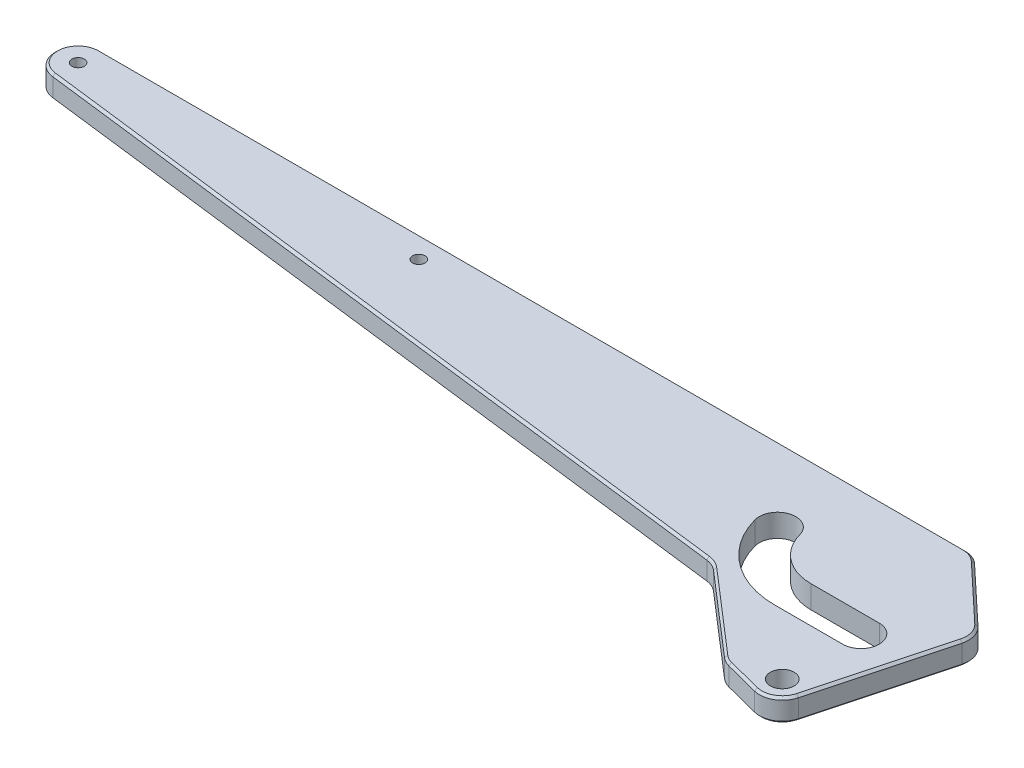
SolidWorks part; units mm, degrees
ref_plane "Front Plane" through (0, 0, 0) normal (0, 0, 1) x (1, 0, 0)
ref_plane "Top Plane" through (0, 0, 0) normal (0, 1, 0) x (1, 0, 0)
ref_plane "Right Plane" through (0, 0, 0) normal (1, 0, 0) x (0, 0, -1)
sketch "Sketch1" plane through (0, 0, 0) normal (0, 1, 0) x (1, 0, 0)
  line L3 (-390, 90) -> (34.4682, 90)
  line L4 (-391.2187, 70.0745) -> (-60, 29.406)
  line L5 (9.6593, -2.5882) -> (34.4682, 90)
  line L6 (-2.499, -9.6827) -> (-20, -5.1659)
  line L7 (-20, -5.1659) -> (-60, 29.406)
  arc A2 (-2.499, -9.6827) -> (9.6593, -2.5882) centre (0, 0) ccw
  arc A3 (-390, 90) -> (-391.2187, 70.0745) centre (-390, 80) ccw
  dimension "D1" = 20
  dimension "D2" = 390
  dimension "D3" = 80
  dimension "D4" = 7
  dimension "D5" = 75
  dimension "D6" = 20
  dimension "D7" = 40
extrude "Boss-Extrude1" add sketch "Sketch1" along normal mid plane 10
sketch "Slot Path" plane through (0, 0, 0) normal (0, 1, 0) x (1, 0, 0)
  line L0 (-30, 34.641) -> (0, 34.641)
  line L1 (0, -5.5) -> (0, 5.5) construction
  line L2 (-5.5, 0) -> (5.5, 0) construction
  arc A0 (-30, 34.641) -> (-58.9778, 56.8764) centre (-30, 64.641) cw
  dimension "D1" = 30
  dimension "D2" = 34.641
sketch "Sketch4" plane through (0, 5, 0) normal (0, 1, 0) x (1, 0, 0)
  line L30 (-30, 26.591) -> (0, 26.591)
  line L31 (-30, 42.691) -> (0, 42.691)
  arc A52 (-66.7535, 54.793) -> (-30, 26.591) centre (-30, 64.641) ccw
  arc A53 (-51.2021, 58.9599) -> (-30, 42.691) centre (-30, 64.641) ccw
  arc A54 (-66.7535, 54.793) -> (-51.2021, 58.9599) centre (-58.9778, 56.8764) cw
  arc A55 (0, 26.591) -> (0, 42.691) centre (0, 34.641) ccw
extrude "Slot" cut sketch "Sketch4" against normal through all
hole_wizard "Ø10.5 (10.5) Diameter Hole1" positions "Sketch9" profile "Sketch10" hole size "Ø10.5" standard "ANSI Metric"
sketch "Sketch9" plane through (0, 5, 0) normal (0, 1, 0) x (1, 0, 0)
  point P0 (0, 0)
sketch "Sketch10" plane through (0, 5, 0) normal (1, 0, 0) x (0, 0, 1)
  line L0 (0, 0) -> (0, 18.1545)
  line L1 (0, 18.1545) -> (5.25, 15)
  line L2 (5.25, 15) -> (5.25, 0)
  line L5 (5.25, 0) -> (0, 0)
  line L10 (0, 18.1545) -> (-5.25, 15) construction
  line L11 (0, -6.35) -> (0, 107.95) construction
  dimension "Hole Dia." = 10.5
  dimension "Hole Depth" = 15
  dimension "Drill Angle" = 118
hole_wizard "CBORE for M5 SHCS2" positions "Sketch14" profile "Sketch15" counterbore size "M5" standard "ANSI Metric"
sketch "Sketch14" plane through (0, -5, 0) normal (0, -1, 0) x (-1, 0, 0)
  arc A0 (391.2187, 70.0745) -> (390, 90) centre (390, 80) ccw construction
  point P0 (390, 80)
  point P2 (240, 80)
  dimension "D1" = 150
sketch "Sketch15" plane through (-390, -5, -80) normal (1, 0, 0) x (0, 0, -1)
  line L0 (0, 0) -> (0, 23.2524)
  line L1 (0, 23.2524) -> (2.75, 21.6)
  line L2 (2.75, 21.6) -> (2.75, 5)
  line L3 (2.75, 5) -> (5, 5)
  line L4 (5, 5) -> (5, 0)
  line L5 (5, 0) -> (0, 0)
  line L10 (0, 23.2524) -> (-2.75, 21.6) construction
  line L11 (0, -6.35) -> (0, 107.95) construction
  dimension "Hole Dia." = 5.5
  dimension "Hole Depth" = 21.6
  dimension "C'Bore Dia." = 10
  dimension "C'Bore Depth" = 5
  dimension "Drill Angle" = 118
sketch "Sketch13" plane through (0, 5, 0) normal (0, 1, 0) x (1, 0, 0)
  line L0 (-5.5318, 90) -> (34.4682, 90)
  line L1 (34.4682, 90) -> (-390, 90) construction
  line L2 (9.6593, -2.5882) -> (34.4682, 90) construction
  line L3 (34.4682, 90) -> (26.4297, 60)
  line L4 (26.4297, 60) -> (-5.5318, 90)
  dimension "D1" = 30
  dimension "D2" = 40
extrude "Cut-Extrude3" cut sketch "Sketch13" against normal through all
fillet "Fillet1" radius 10 4 edges at (-5.5318, 0, -90) (26.4297, 0, -60) (-20, 0, 5.1659) (-60, 0, -29.406)
chamfer "Chamfer1" distance 1 angle 45 24 edges at (-10.1155, -5, 7.717) (-19.8744, -5, 4.9261) (-39.7354, -5, -11.8914) (-60.1834, -5, -28.9925) (-227.1189, -5, -49.9256) (-399.9813, -5, -80.6105) (-199.7449, -5, -90) (-5.8096, -5, -89.2982) (9.7094, -5, -75.6941) (24.8381, -5, -59.5464) (17.2698, -5, -25.8147) (5.0399, -5, 8.6371) (-399.9813, 5, -80.6105) (-227.1189, 5, -49.9256) (-60.1834, 5, -28.9925) (-39.7354, 5, -11.8914) (-19.8744, 5, 4.9261) (-10.1155, 5, 7.717) (5.0399, 5, 8.6371) (17.2698, 5, -25.8147) (24.8381, 5, -59.5464) (9.7094, 5, -75.6941) (-5.8096, 5, -89.2982) (-199.7449, 5, -90)
